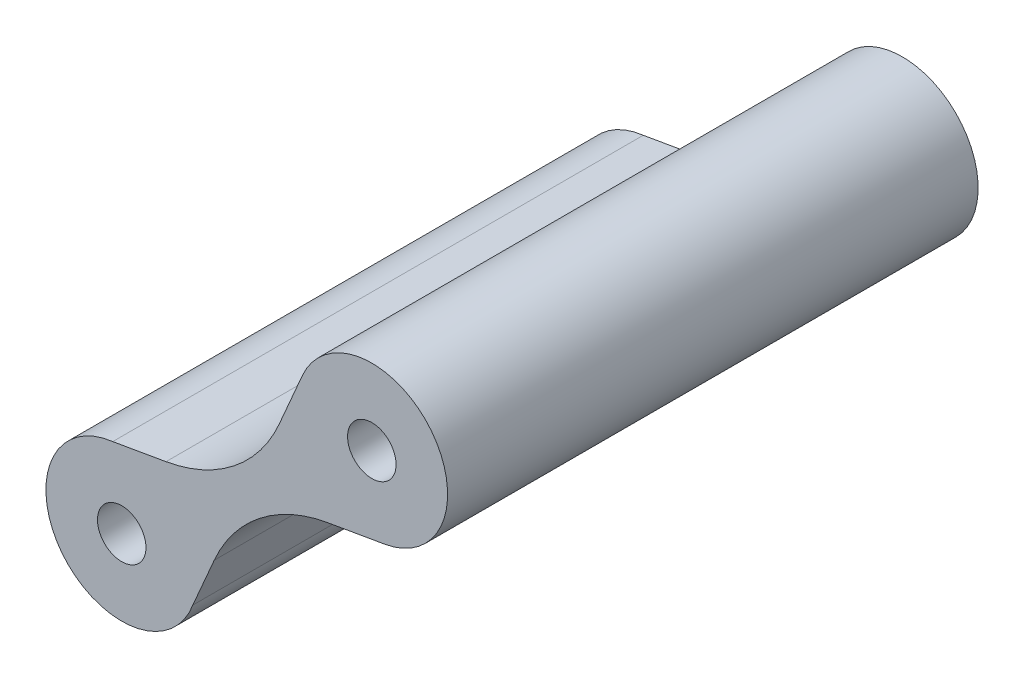
SolidWorks part; units mm, degrees
ref_plane "Front Plane" through (0, 0, 0) normal (0, 0, 1) x (1, 0, 0)
ref_plane "Top Plane" through (0, 0, 0) normal (0, 1, 0) x (1, 0, 0)
ref_plane "Right Plane" through (0, 0, 0) normal (1, 0, 0) x (0, 0, -1)
sketch "Sketch1" plane through (0, 0, 0) normal (0, 0, 1) x (-1, 0, 0)
  line L0 (16.5, 0) -> (0, -13) construction
  line L1 (0, -13) -> (3.0933, -16.9261) construction
  line L2 (13.5775, -5.5751) -> (17.0945, -4.9645)
  line L3 (19.5944, -3.9275) -> (16.5, 0) construction
  line L4 (16.5, 0) -> (13.4056, 3.9275) construction
  line L5 (6.107, -11.4644) -> (4.583, -14.9948)
  line L6 (-3.0933, -9.0739) -> (0, -13) construction
  line L7 (2.9219, -7.4219) -> (-0.867, -8.0775)
  line L8 (10.3958, -1.5368) -> (11.8124, 1.7396)
  circle A0 centre (16.5, 0) radius 5
  circle A1 centre (0, -13) radius 4.9983
  arc A2 (2.9219, -7.4219) -> (10.3958, -1.5368) centre (1.217, 2.4317) ccw
  arc A3 (6.107, -11.4644) -> (13.5775, -5.5751) centre (15.288, -15.4277) cw
  circle A4 centre (0, -13) radius 1.6
  circle A5 centre (16.5, 0) radius 1.6
  point P7 (8.25, -6.5)
  point P14 (0, 0)
  point P17 (8.25, -6.5)
  point P18 (0, 0)
  point P19 (-0.867, -8.0775)
  point P20 (0, 0)
  point P21 (11.8124, 1.7396)
  dimension "D1" = 10
extrude "Boss-Extrude1" add sketch "Sketch1" along normal blind 35
